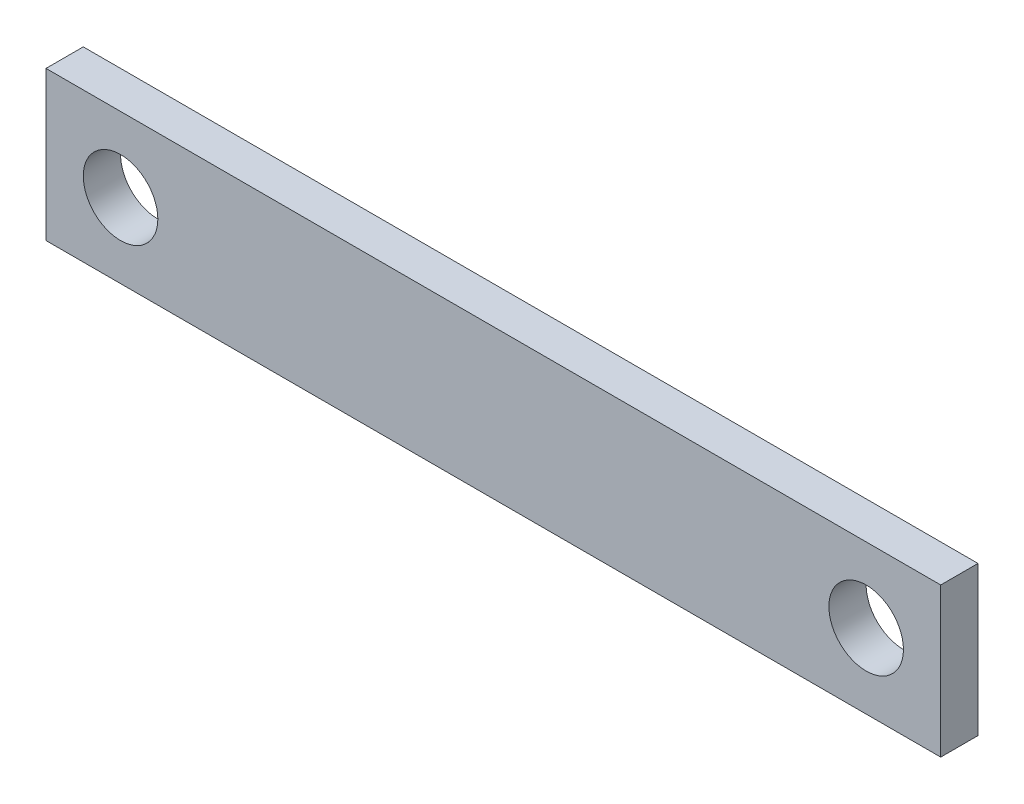
SolidWorks part; units mm, degrees
material "6061-T6 (SS)"
ref_plane "Front Plane" through (0, 0, 0) normal (0, 0, 1) x (1, 0, 0)
ref_plane "Top Plane" through (0, 0, 0) normal (0, 1, 0) x (1, 0, 0)
ref_plane "Right Plane" through (0, 0, 0) normal (1, 0, 0) x (0, 0, -1)
sketch "Sketch1" plane through (0, 0, 0) normal (0, 0, 1) x (1, 0, 0)
  line L0 (0, 0) -> (0, 12.7)
  line L1 (0, 12.7) -> (76.2, 12.7)
  line L2 (76.2, 12.7) -> (76.2, 0)
  line L3 (76.2, 0) -> (0, 0)
  circle A0 centre (6.35, 6.35) radius 3.175
  circle A1 centre (69.85, 6.35) radius 3.175
  point P9 (76.2, 6.35)
  dimension "D2" = 6.35
  dimension "D4" = 6.35
  dimension "D8" = 6.35
  dimension "D1" = 63.5
  dimension "D3" = 6.35
  dimension "D5" = 12.7
  dimension "D6" = 6.35
  dimension "D7" = 6.35
extrude "Boss-Extrude1" add sketch "Sketch1" along normal blind 3.175
